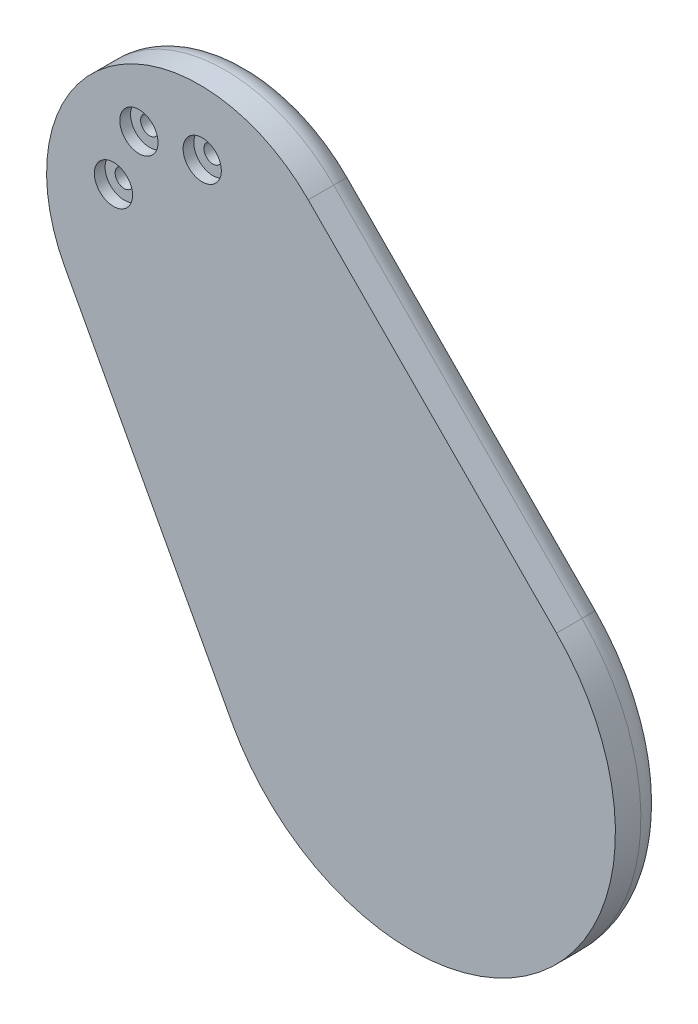
SolidWorks part; units mm, degrees
ref_plane "Front Plane" through (0, 0, 0) normal (0, 0, 1) x (1, 0, 0)
ref_plane "Top Plane" through (0, 0, 0) normal (0, 1, 0) x (1, 0, 0)
ref_plane "Right Plane" through (0, 0, 0) normal (1, 0, 0) x (0, 0, -1)
sketch "Sketch3" plane through (0, 0, -6.35) normal (0, 0, 1) x (1, 0, 0)
  circle A0 centre (0, 0) radius 6.35
  dimension "D1" = 12.7
extrude "Boss-Extrude2" add sketch "Sketch3" along normal blind 5.08 and the other way up to surface (9.525 mm away)
sketch "Sketch4" plane through (0, 0, -1.27) normal (0, 0, 1) x (1, 0, 0)
  line L0 (-44.7501, -24.0431) -> (-86.394, 53.4663)
  line L1 (-25.738, 98.2859) -> (36.1245, 35.7164)
  arc A0 (-44.7501, -24.0431) -> (36.1245, 35.7164) centre (0, 0) ccw
  arc A1 (-25.738, 98.2859) -> (-86.394, 53.4663) centre (-52.8314, 71.4986) ccw
  dimension "D1" = 50.8
extrude "Boss-Extrude3" add sketch "Sketch4" along normal blind 12.7
sketch "Sketch5" plane through (0, 0, -1.27) normal (0, 0, -1) x (-1, 0, 0)
  circle A0 centre (52.8314, 71.4986) radius 3.175
  dimension "D1" = 6.35
extrude "Boss-Extrude4" add sketch "Sketch5" along normal up to surface (10.16 mm away)
sketch "Sketch6" plane through (0, 0, -1.27) normal (0, 0, -1) x (-1, 0, 0)
  circle A0 centre (0, 0) radius 6.35 construction
  circle A1 centre (0, 0) radius 6.35
  circle A5 centre (0, 0) radius 13.8887 construction
  circle A6 centre (0, 0) radius 13.8887
extrude "Boss-Extrude5" add sketch "Sketch6" along normal up to surface (8.255 mm away)
sketch "Sketch7" plane through (0, 0, -1.27) normal (0, 0, -1) x (-1, 0, 0)
  circle A0 centre (52.8314, 71.4986) radius 3.175 construction
  circle A1 centre (52.8314, 71.4986) radius 3.175
  circle A2 centre (52.8314, 71.4986) radius 7.6378 construction
  circle A3 centre (52.8314, 71.4986) radius 7.6378
extrude "Boss-Extrude6" add sketch "Sketch7" along normal up to surface (5.1816 mm away)
fillet "Fillet3" radius 6.35 4 edges at (5.1933, 67.0011, -1.27) (30.1894, -40.8563, -1.27) (-65.572, 14.7116, -1.27) (-75.4735, 102.1409, -1.27)
fillet "Fillet4" radius 2.54 2 edges at (13.8887, 0, -1.27) (-45.1936, 71.4986, -1.27)
fillet "Fillet1" radius 0.635 2 edges at (6.35, 0, -15.875) (-49.6564, 71.4986, -11.43)
fillet "Fillet5" radius 0.254 2 edges at (-13.8887, 0, -9.525) (-60.4692, 71.4986, -6.4516)
hole_wizard "CBORE for #8 Binding Head Machine Screw1" positions "Sketch8" profile "Sketch9" counterbore size "#8" standard "ANSI Inch"
sketch "Sketch8" plane through (0, 0, 11.43) normal (0, 0, 1) x (1, 0, 0)
  line L0 (-58.4919, 79.1592) -> (-75.4735, 102.1409) construction
  line L2 (-58.4919, 79.1592) -> (-45.5389, 108.8942) construction
  circle A3 centre (-58.4919, 79.1592) radius 15.875
  circle A4 centre (-58.4919, 79.1592) radius 15.875 construction
  arc A5 (-25.738, 98.2859) -> (-86.394, 53.4663) centre (-52.8314, 71.4986) ccw construction
  point P0 (-52.1519, 93.7132)
  point P2 (-67.9261, 91.9268)
  point P35 (-74.2661, 77.3727)
  dimension "D2" = 60
  dimension "D1" = 6.35
sketch "Sketch9" plane through (-52.1519, 93.7132, 11.43) normal (1, 0, 0) x (0, -1, 0)
  line L0 (0, 0) -> (0, 14.0507)
  line L1 (0, 14.0507) -> (2.2479, 12.7)
  line L2 (2.2479, 12.7) -> (2.2479, 2.667)
  line L3 (2.2479, 2.667) -> (4.7625, 2.667)
  line L4 (4.7625, 2.667) -> (4.7625, 0)
  line L5 (4.7625, 0) -> (0, 0)
  line L10 (0, 14.0507) -> (-2.2479, 12.7) construction
  line L11 (0, -6.35) -> (0, 107.95) construction
  dimension "Hole Dia." = 4.4958
  dimension "Hole Depth" = 12.7
  dimension "C'Bore Dia." = 9.525
  dimension "C'Bore Depth" = 2.667
  dimension "Drill Angle" = 118
